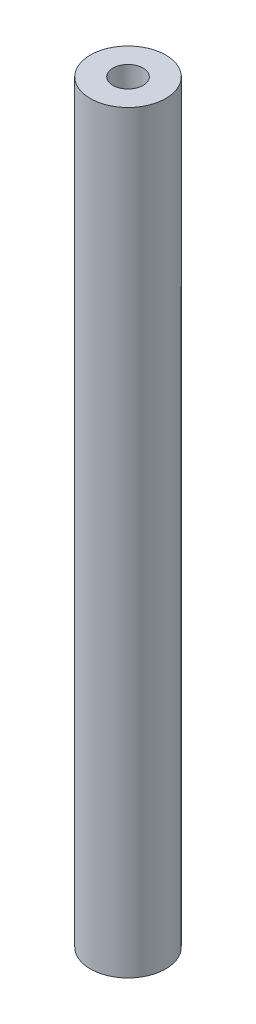
SolidWorks part; units mm, degrees
material "Glass"
ref_plane "Front Plane" through (0, 0, 0) normal (0, 0, 1) x (1, 0, 0)
ref_plane "Top Plane" through (0, 0, 0) normal (0, 1, 0) x (1, 0, 0)
ref_plane "Right Plane" through (0, 0, 0) normal (1, 0, 0) x (0, 0, -1)
sketch "Sketch1" plane through (0, 0, 0) normal (0, 0, 1) x (1, 0, 0)
  line L0 (0, 0) -> (0, 45.6956) construction
  line L1 (0, 0) -> (0.6, 0) construction
  line L3 (0.6, 0) -> (1.5, 0)
  line L4 (0.6, 0) -> (0.6, 30)
  line L5 (0.6, 30) -> (1.5, 30)
  line L6 (1.5, 0) -> (1.5, 30)
  dimension "D1" = 1.2
  dimension "D2" = 3
  dimension "D3" = 30
revolve "Revolve1" add sketch "Sketch1" angle 360 about L0
